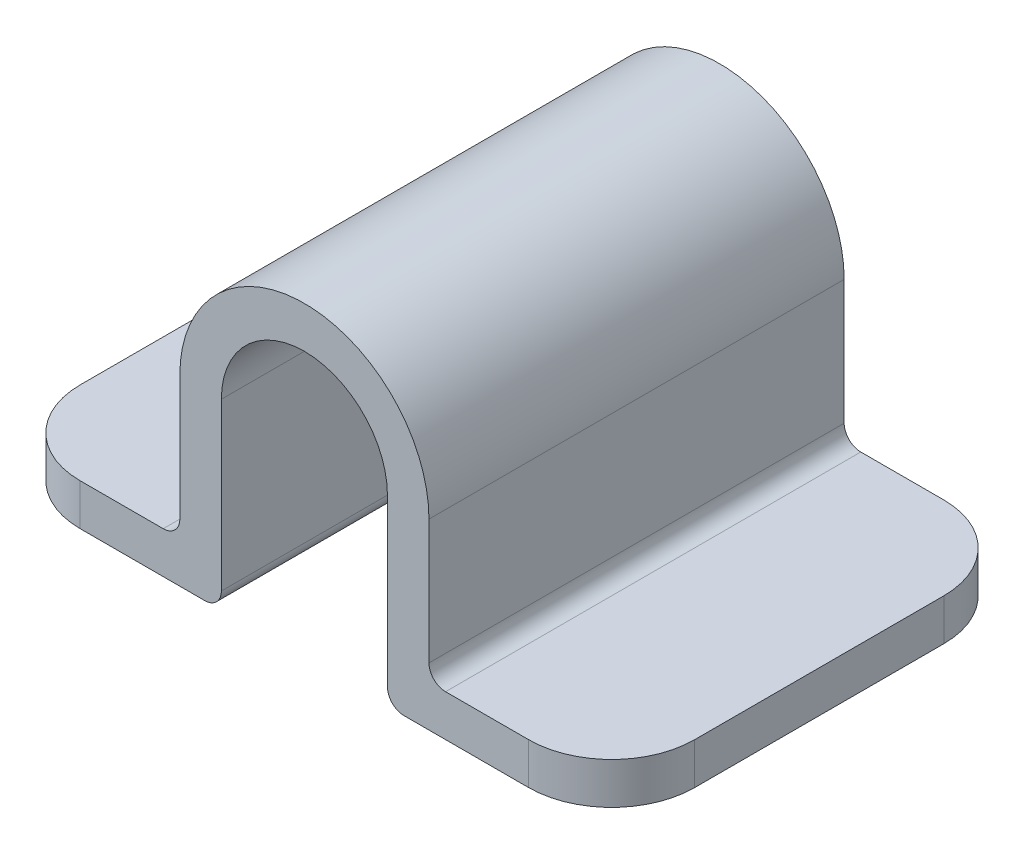
SolidWorks part; units mm, degrees
material "AISI 1020"
ref_plane "Front Plane" through (0, 0, 0) normal (0, 0, 1) x (1, 0, 0)
ref_plane "Top Plane" through (0, 0, 0) normal (0, 1, 0) x (1, 0, 0)
ref_plane "Right Plane" through (0, 0, 0) normal (1, 0, 0) x (0, 0, -1)
sketch "Sketch6" plane through (0, 0, 0) normal (0, 0, 1) x (1, 0, 0)
  line L0 (10, 0) -> (10, -20)
  line L1 (12, -22) -> (37, -22)
  line L2 (0, 3.3383) -> (0, -3.3383) construction
  line L3 (-12, -22) -> (-37, -22)
  line L4 (-10, 0) -> (-10, -20)
  line L5 (17, -17) -> (37, -17)
  line L6 (15, 0) -> (15, -15)
  line L7 (-15, 0) -> (-15, -15)
  line L8 (-17, -17) -> (-37, -17)
  line L9 (15, -17) -> (37, -17) construction
  line L10 (15, 0) -> (15, -17) construction
  line L11 (-15, -17) -> (-37, -17) construction
  line L12 (-15, 0) -> (-15, -17) construction
  line L13 (-37, -22) -> (-37, -17)
  line L14 (37, -17) -> (37, -22)
  arc A0 (10, 0) -> (-10, 0) centre (0, 0) ccw
  arc A1 (10, -20) -> (12, -22) centre (12, -20) ccw
  arc A2 (-10, -20) -> (-12, -22) centre (-12, -20) cw
  arc A3 (-17, -17) -> (-15, -15) centre (-17, -15) ccw
  arc A4 (15, 0) -> (-15, 0) centre (0, 0) ccw
  arc A6 (17, -17) -> (15, -15) centre (17, -15) cw
  arc A7 (15, -17) -> (15, -17) centre (15, -17) ccw construction
  arc A8 (-15, -17) -> (-15, -17) centre (-15, -17) cw construction
  point P14 (0, 0)
  dimension "D1" = 20
  dimension "D4" = 2
  dimension "D6" = 2
  dimension "D2" = 20
  dimension "D3" = 25
  dimension "D5" = 5
extrude "Boss-Extrude4" add sketch "Sketch6" against normal blind 50 contours L6 A6 L5 L14 L1 A1 L0 A0 L4 A2 L3 L13 L8 A3 L7 A4
fillet "Fillet1" radius 10 4 edges at (37, -19.5, 0) (37, -19.5, -50) (-37, -19.5, 0) (-37, -19.5, -50)
